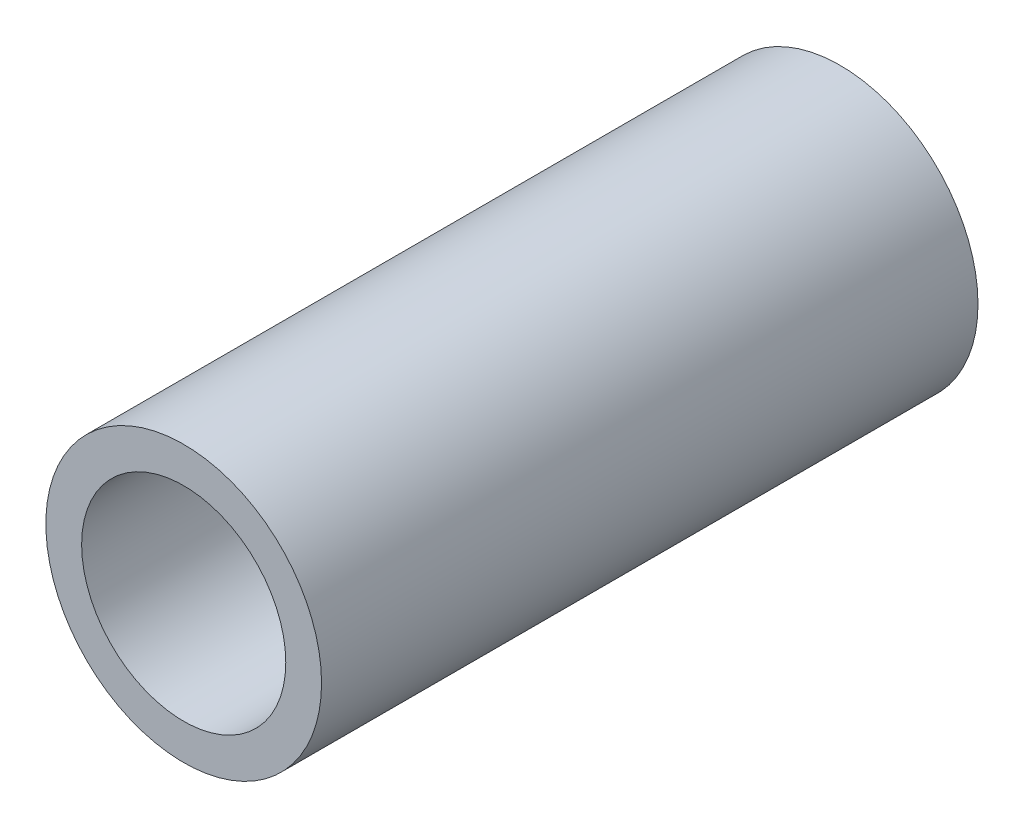
SolidWorks part; units mm, degrees
material "AISI 316 Stainless Steel Sheet (SS)"
ref_plane "Front Plane" through (0, 0, 0) normal (0, 0, 1) x (1, 0, 0)
ref_plane "Top Plane" through (0, 0, 0) normal (0, 1, 0) x (1, 0, 0)
ref_plane "Right Plane" through (0, 0, 0) normal (1, 0, 0) x (0, 0, -1)
sketch "Sketch1" plane through (0, 0, 0) normal (0, 0, 1) x (1, 0, 0)
  circle A0 centre (0, 0) radius 7.8994
  circle A1 centre (0, 0) radius 10.668
  dimension "D1" = 2.7686
  dimension "D2" = 21.336
extrude "Boss-Extrude1" add sketch "Sketch1" along normal blind 50.8
